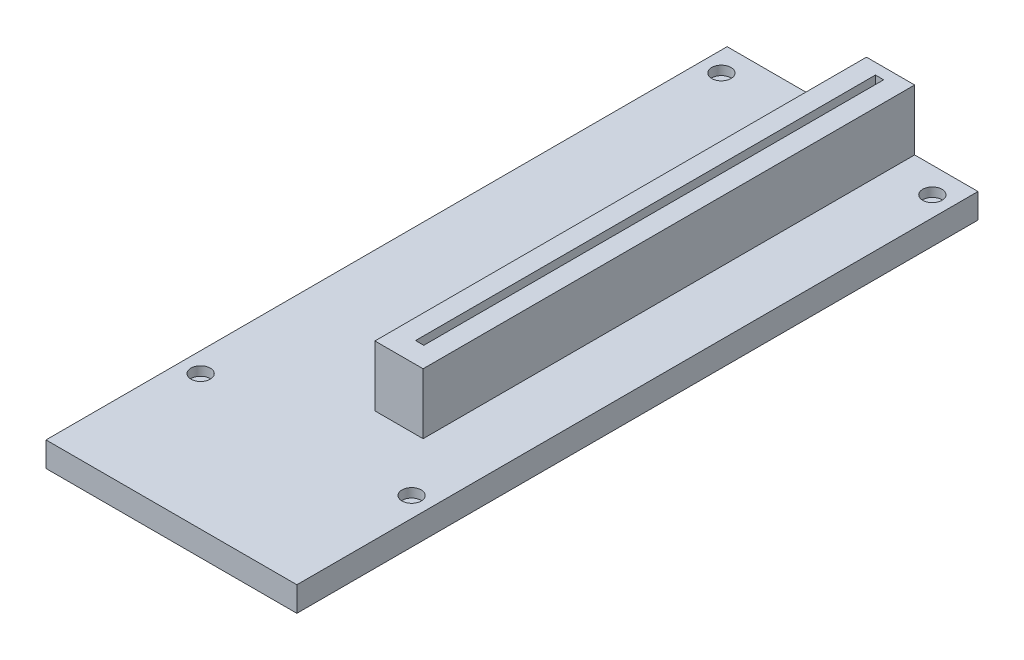
SolidWorks part; units mm, degrees
ref_plane "Front Plane" through (0, 0, 0) normal (0, 0, 1) x (1, 0, 0)
ref_plane "Top Plane" through (0, 0, 0) normal (0, 1, 0) x (1, 0, 0)
ref_plane "Right Plane" through (0, 0, 0) normal (1, 0, 0) x (0, 0, -1)
sketch "Sketch1" plane through (0, 0, 0) normal (0, 1, 0) x (1, 0, 0)
  line L0 (-226.1194, 569.0017) -> (616.7002, 598.4336) construction
  line L1 (-22.775, -61.835) -> (22.775, -61.835)
  line L2 (-22.775, -61.835) -> (-22.775, 61.835)
  line L3 (-22.775, 61.835) -> (22.775, 61.835)
  line L4 (22.775, -61.835) -> (22.775, 61.835)
  line L5 (-22.775, -61.835) -> (22.775, 61.835) construction
  line L6 (-22.775, 61.835) -> (22.775, -61.835) construction
  line L7 (-863.0534, -760.2221) -> (-31.0534, -760.2221) construction
  line L8 (0, -61.835) -> (0, 61.835) construction
  circle A0 centre (-19.1543, -37.3795) radius 1.75
  circle A1 centre (-19.1543, 57.1711) radius 1.75
  circle A2 centre (19.1543, -37.3795) radius 1.75
  circle A3 centre (19.1543, 57.1711) radius 1.75
  point P0 (0, 0)
  dimension "D1" = 123.67
  dimension "D2" = 45.55
extrude "Boss-Extrude1" add sketch "Sketch1" along normal blind 1.65
sketch "Sketch2" plane through (0, 0, 0) normal (0, -1, 0) x (1, 0, 0)
  line L4 (22.775, -61.835) -> (22.775, 61.835)
  line L5 (22.775, 61.835) -> (-22.775, 61.835)
  line L6 (-22.775, 61.835) -> (-22.775, -61.835)
  line L7 (-22.775, -61.835) -> (22.775, -61.835)
  line L8 (22.775, -61.835) -> (22.775, 61.835)
  line L9 (22.775, 61.835) -> (-22.775, 61.835)
  line L10 (-22.775, 61.835) -> (-22.775, -61.835)
  line L11 (-22.775, -61.835) -> (22.775, -61.835)
  dimension "D1" = 0
extrude "Boss-Extrude2" add sketch "Sketch2" along normal blind 2.85
sketch "Sketch3" plane through (0, 1.65, 0) normal (0, 1, 0) x (1, 0, 0)
  line L0 (22.775, -61.835) -> (22.775, 61.835) construction
  line L1 (2.525, 61.835) -> (11.275, 61.835)
  line L2 (2.525, 61.835) -> (2.525, -27.415)
  line L3 (2.525, -27.415) -> (11.275, -27.415)
  line L4 (11.275, 61.835) -> (11.275, -27.415)
  line L5 (22.775, 61.835) -> (-22.775, 61.835) construction
  point P6 (0, 0)
  dimension "D1" = 11.5
  dimension "D2" = 89.25
  dimension "D3" = 8.75
extrude "Boss-Extrude3" add sketch "Sketch3" along normal blind 11 contours L2 L1 L4 L3
sketch "Sketch4" plane through (0, 12.65, 0) normal (0, 1, 0) x (1, 0, 0)
  line L0 (2.525, 61.835) -> (11.275, 61.835) construction
  line L1 (6.15, 59.835) -> (7.65, 59.835)
  line L2 (6.15, 59.835) -> (6.15, -23.665)
  line L3 (6.15, -23.665) -> (7.65, -23.665)
  line L4 (7.65, 59.835) -> (7.65, -23.665)
  line L5 (6.9, 61.835) -> (6.9, -27.415) construction
  line L6 (2.525, -27.415) -> (11.275, -27.415) construction
  point P10 (6.9, 59.835)
  dimension "D1" = 83.5
  dimension "D2" = 1.5
  dimension "D3" = 2
extrude "Cut-Extrude1" cut sketch "Sketch4" against normal blind 7
